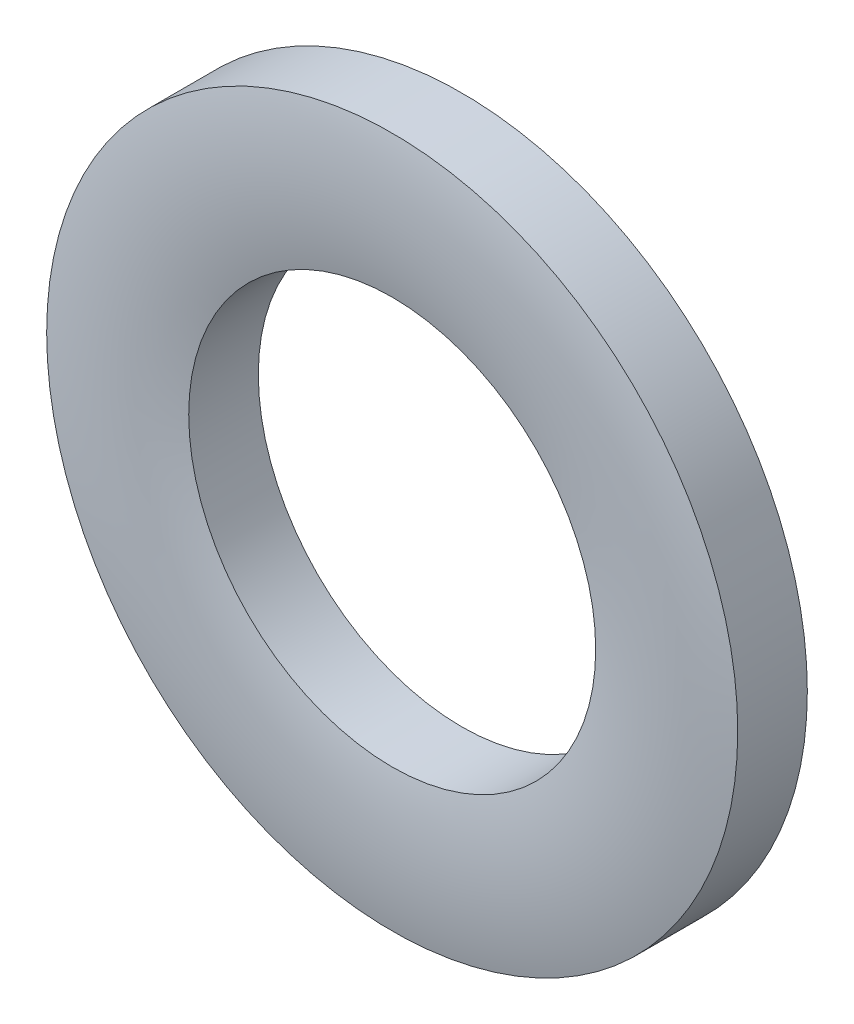
SolidWorks part; units mm, degrees
ref_plane "Front Plane" through (0, 0, 0) normal (0, 0, 1) x (1, 0, 0)
ref_plane "Top Plane" through (0, 0, 0) normal (0, 1, 0) x (1, 0, 0)
ref_plane "Right Plane" through (0, 0, 0) normal (1, 0, 0) x (0, 0, -1)
sketch "Sketch1" plane through (0, 0, 0) normal (0, 0, 1) x (1, 0, 0)
  circle A0 centre (0, 0) radius 2.65
  circle A1 centre (0, 0) radius 4.5
  dimension "ID" = 5.3
  dimension "OD" = 9
sketch "Sketch2" plane through (0, 0, 0) normal (1, 0, 0) x (0, 0, -1)
  line L0 (-0.5, 4.5) -> (0.5, 4.5) construction
  line L1 (-0.5, 0) -> (0.5, 0) construction
  point P2 (0, 4.5)
  dimension "Thickness Range" = 1
sketch "Sketch3" plane through (0, 0, 0) normal (1, 0, 0) x (0, 0, -1)
  line L0 (0.5, 4.5) -> (-0.4063, 4.5)
  line L1 (0.5, 2.65) -> (-0.4063, 2.65)
  line L2 (0.5, 2.65) -> (0.5, 4.5)
  line L3 (-0.5, 4.5) -> (-0.5, 2.65) construction
  arc A0 (-0.4063, 2.65) -> (-0.4063, 4.5) centre (4.1126, 3.575) cw
  point P9 (0, 2.65)
  dimension "D1" = 0.0937
revolve "Revolve1" add sketch "Sketch3" angle 360 about L1
equation "\"D1@Sketch3\"=\"Thickness Range@Sketch2\"*.0937"
